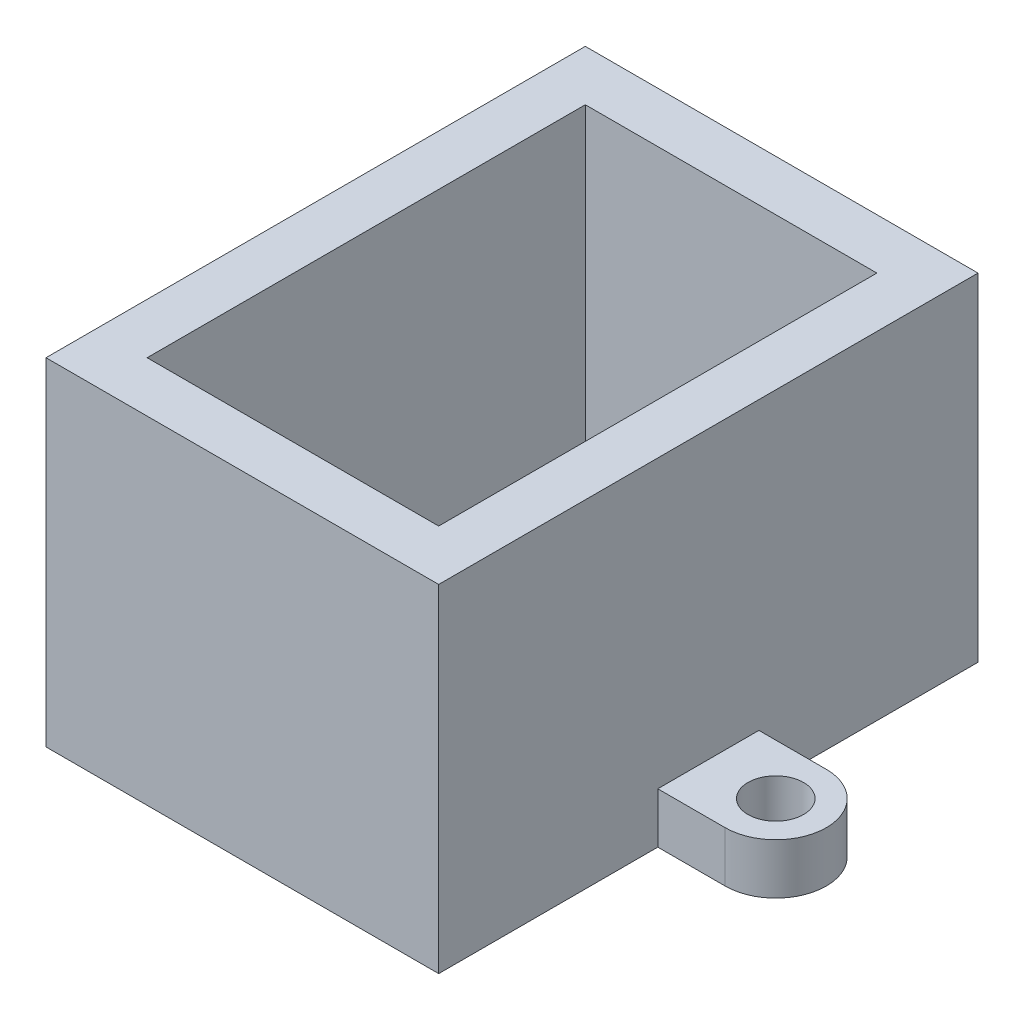
SolidWorks part; units mm, degrees
ref_plane "Front Plane" through (0, 0, 0) normal (0, 0, 1) x (1, 0, 0)
ref_plane "Top Plane" through (0, 0, 0) normal (0, 1, 0) x (1, 0, 0)
ref_plane "Right Plane" through (0, 0, 0) normal (1, 0, 0) x (0, 0, -1)
sketch "Sketch1" plane through (0, 0, 0) normal (0, 1, 0) x (1, 0, 0)
  line L1 (-8.65, 13) -> (8.65, 13)
  line L2 (-8.65, 13) -> (-8.65, -13)
  line L3 (-8.65, -13) -> (8.65, -13)
  line L4 (8.65, 13) -> (8.65, -13)
  line L5 (-8.65, 13) -> (8.65, -13) construction
  line L6 (-8.65, -13) -> (8.65, 13) construction
  line L7 (-11.65, 16) -> (11.65, 16)
  line L8 (-11.65, 16) -> (-11.65, -16)
  line L9 (-11.65, -16) -> (11.65, -16)
  line L10 (11.65, 16) -> (11.65, -16)
  line L11 (-11.65, 16) -> (11.65, -16) construction
  line L12 (-11.65, -16) -> (11.65, 16) construction
  point P0 (0, 0)
  point P5 (0, 0)
  dimension "D1" = 17.3
  dimension "D2" = 26
  dimension "D3" = 32
  dimension "D4" = 23.3
extrude "Boss-Extrude1" add sketch "Sketch1" along normal blind 20
sketch "Sketch3" plane through (0, 0, 0) normal (0, 1, 0) x (1, 0, 0)
  line L0 (-11.65, 3) -> (11.65, 3) construction
  line L1 (-11.65, 16) -> (-11.65, -16) construction
  line L2 (11.65, -16) -> (11.65, 16) construction
  line L3 (11.65, -3) -> (-11.65, -3) construction
  line L4 (11.65, 3) -> (15.65, 3)
  line L5 (15.65, -3) -> (11.65, -3)
  line L6 (-11.65, -3) -> (-15.65, -3)
  line L7 (-15.65, 3) -> (-11.65, 3)
  line L8 (-11.65, 3) -> (-11.65, -3)
  line L9 (11.65, 3) -> (11.65, -3)
  arc A0 (15.65, 3) -> (15.65, -3) centre (15.65, 0) cw
  arc A1 (-15.65, -3) -> (-15.65, 3) centre (-15.65, 0) cw
  circle A2 centre (15.65, 0) radius 1.65
  circle A3 centre (-15.65, 0) radius 1.65
  dimension "D1" = 4
  dimension "D4" = 3.3
  dimension "D2" = 3
  dimension "D3" = 3
extrude "Boss-Extrude2" add sketch "Sketch3" along normal blind 3
